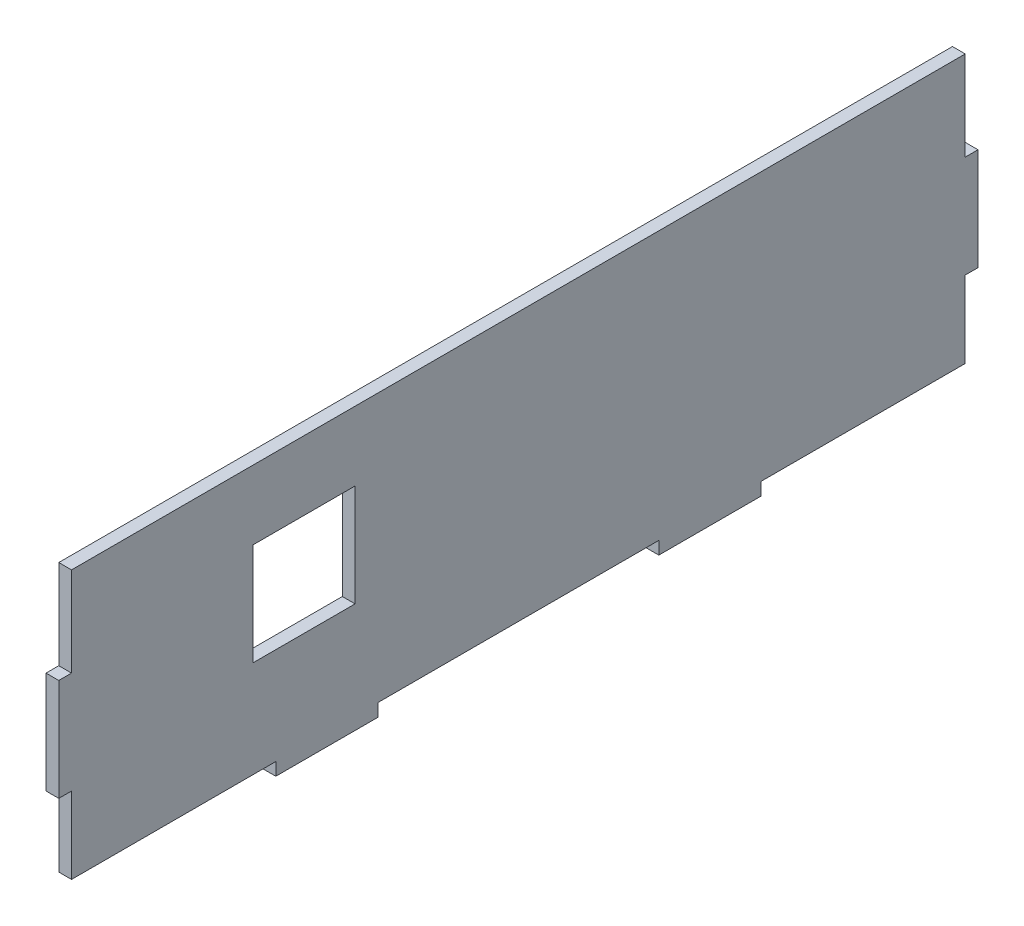
SolidWorks part; units mm, degrees
ref_plane "Front Plane" through (0, 0, 0) normal (0, 0, 1) x (1, 0, 0)
ref_plane "Top Plane" through (0, 0, 0) normal (0, 1, 0) x (1, 0, 0)
ref_plane "Right Plane" through (0, 0, 0) normal (1, 0, 0) x (0, 0, -1)
sketch "Sketch1" plane through (0, 0, 0) normal (1, 0, 0) x (0, 0, -1)
  line L0 (-116.66, 27.079) -> (-116.66, 1.679)
  line L1 (-116.66, 27.079) -> (105.59, 27.079)
  line L2 (-116.66, 1.679) -> (-119.835, 1.679)
  line L3 (-116.66, -42.771) -> (-65.86, -42.771)
  line L4 (-119.835, 1.679) -> (-119.835, -23.721)
  line L5 (-119.835, -23.721) -> (-116.66, -23.721)
  line L6 (-116.66, -23.721) -> (-116.66, -42.771)
  line L7 (105.59, 27.079) -> (105.59, 1.679)
  line L8 (105.59, 1.679) -> (108.765, 1.679)
  line L9 (108.765, 1.679) -> (108.765, -23.721)
  line L10 (108.765, -23.721) -> (105.59, -23.721)
  line L11 (105.59, -23.721) -> (105.59, -42.771)
  line L12 (-65.86, -42.771) -> (-65.86, -45.946)
  line L13 (-65.86, -45.946) -> (-40.46, -45.946)
  line L14 (-40.46, -45.946) -> (-40.46, -42.771)
  line L15 (-40.46, -42.771) -> (29.39, -42.771)
  line L16 (29.39, -42.771) -> (29.39, -45.946)
  line L17 (29.39, -45.946) -> (54.79, -45.946)
  line L18 (54.79, -45.946) -> (54.79, -42.771)
  line L19 (54.79, -42.771) -> (105.59, -42.771)
  dimension "D1" = 222.25
  dimension "D2" = 25.4
  dimension "D3" = 25.4
  dimension "D4" = 3.175
  dimension "D5" = 3.175
  dimension "D6" = 3.175
  dimension "D7" = 19.05
  dimension "D8" = 25.4
  dimension "D9" = 25.4
  dimension "D10" = 50.8
  dimension "D11" = 50.8
  dimension "D12" = 3.175
  dimension "D13" = 69.85
  dimension "D14" = 3.175
  dimension "D15" = 3.175
  dimension "D16" = 3.175
  dimension "D17" = 25.4
  dimension "D18" = 25.4
extrude "Boss-Extrude1" add sketch "Sketch1" along normal blind 3.175
sketch "Sketch2" plane through (3.175, 0, 0) normal (1, 0, 0) x (0, 0, -1)
  line L0 (105.59, 1.679) -> (105.59, 27.079) construction
  line L1 (-116.66, 27.079) -> (105.59, 27.079)
  line L2 (-116.66, 27.079) -> (-116.66, 23.904)
  line L3 (-116.66, 23.904) -> (105.59, 23.904)
  line L4 (105.59, 27.079) -> (105.59, 23.904)
  dimension "D1" = 3.175
extrude "Cut-Extrude1" cut sketch "Sketch2" against normal through all
sketch "Sketch3" plane through (0, 0, 0) normal (-1, 0, 0) x (0, 0, 1)
  line L1 (46.144, 6.7241) -> (71.544, 6.7241)
  line L2 (46.144, 6.7241) -> (46.144, -18.6759)
  line L3 (46.144, -18.6759) -> (71.544, -18.6759)
  line L4 (71.544, 6.7241) -> (71.544, -18.6759)
  dimension "D1" = 25.4
  dimension "D2" = 25.4
extrude "Cut-Extrude2" cut sketch "Sketch3" against normal blind 10
